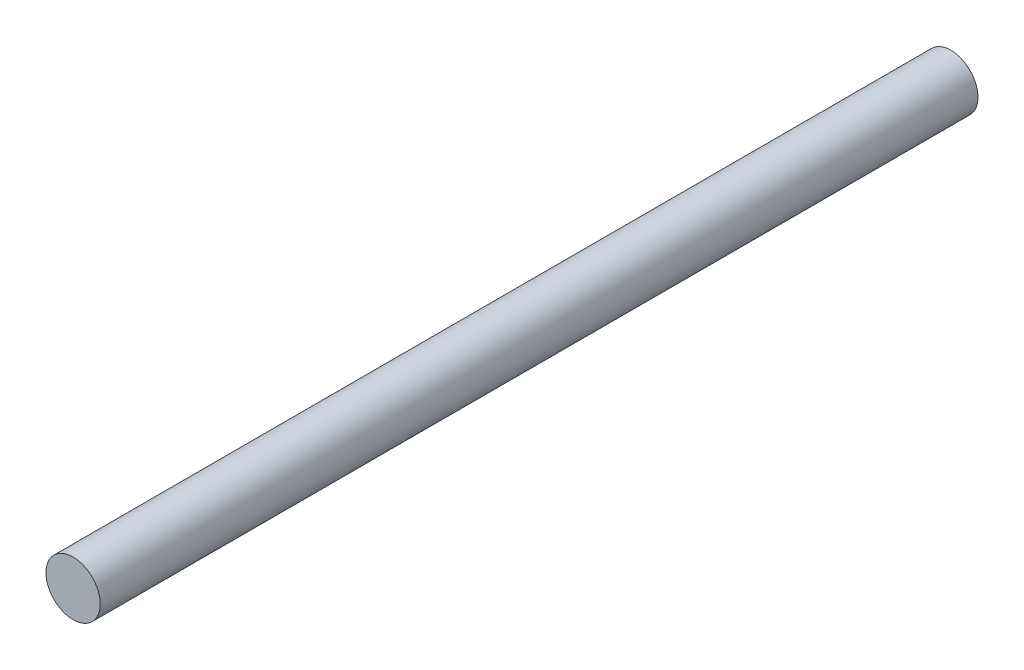
SolidWorks part; units mm, degrees
material "AISI 304"
ref_plane "前视基准面" through (0, 0, 0) normal (0, 0, 1) x (1, 0, 0)
ref_plane "上视基准面" through (0, 0, 0) normal (0, 1, 0) x (1, 0, 0)
ref_plane "右视基准面" through (0, 0, 0) normal (1, 0, 0) x (0, 0, -1)
sketch "Sketch1" plane through (0, 0, 0) normal (0, 0, 1) x (1, 0, 0)
  circle A0 centre (0, 0) radius 3
  dimension "D1" = 6
extrude "Boss-Extrude1" add sketch "Sketch1" along normal blind 97
